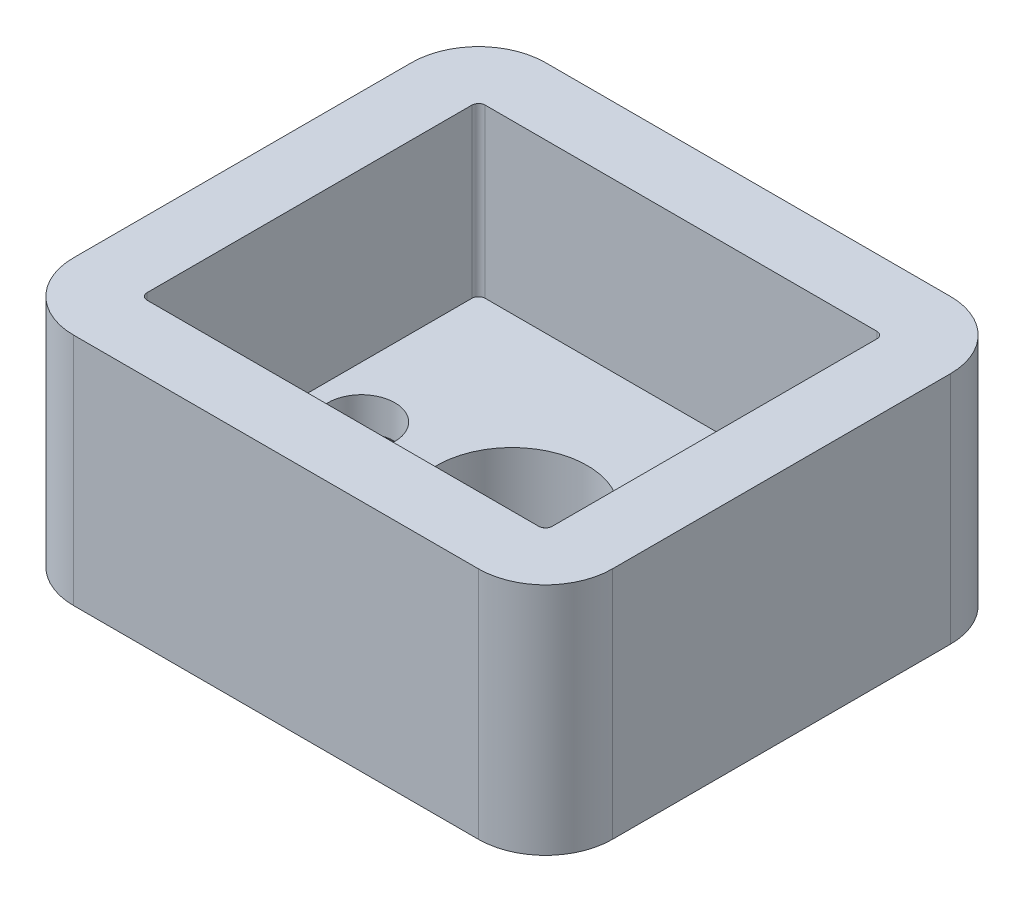
SolidWorks part; units mm, degrees
ref_plane "Front Plane" through (0, 0, 0) normal (0, 0, 1) x (1, 0, 0)
ref_plane "Top Plane" through (0, 0, 0) normal (0, 1, 0) x (1, 0, 0)
ref_plane "Right Plane" through (0, 0, 0) normal (1, 0, 0) x (0, 0, -1)
sketch "Sketch1" plane through (0, 0, 0) normal (0, 1, 0) x (1, 0, 0)
  line L0 (0, 5.05) -> (0, 7.05) construction
  line L1 (-8.05, 7.05) -> (8.05, 7.05)
  line L2 (-8.05, 7.05) -> (-8.05, -7.05)
  line L3 (-8.05, -7.05) -> (8.05, -7.05)
  line L4 (8.05, 7.05) -> (8.05, -7.05)
  line L5 (0, -5.05) -> (0, 0) construction
  line L6 (-8.05, 0) -> (-6.05, 0) construction
  line L11 (0, -5.05) -> (0, 0) construction
  line L12 (0, 0) -> (6.05, 0) construction
  line L13 (0, 0) -> (6.05, 0) construction
  point P4 (0, 0)
  point P233 (0, 0)
  point P296 (0, 0)
  dimension "D1" = 16.1
  dimension "D2" = 14.1
extrude "Boss-Extrude1" add sketch "Sketch1" along normal blind 7
sketch "Sketch3" plane through (0, 7, 0) normal (0, 1, 0) x (1, 0, 0)
  line L0 (-3.85, 0) -> (3.85, 0) construction
  line L1 (-6.05, 5.05) -> (6.05, 5.05)
  line L2 (-6.05, 5.05) -> (-6.05, -5.05)
  line L3 (-6.05, -5.05) -> (6.05, -5.05)
  line L4 (6.05, 5.05) -> (6.05, -5.05)
  line L5 (0, -5.05) -> (0, 5.05) construction
  line L6 (-6.05, 0) -> (6.05, 0) construction
  line L7 (0, -3.85) -> (0, 3.85) construction
  point P4 (0, 0)
  point P316 (0, 0)
  dimension "D1" = 10.1
  dimension "D2" = 12.1
extrude "Cut-Extrude1" cut sketch "Sketch3" against normal offset from surface (5 mm away) 2 up to plane "Top Plane"
hole_wizard "CSK for M1.6 Countersunk Flat Head Screw1" positions "Sketch6" profile "Sketch7" countersink size "M1.6" standard "ISO" end condition up to next
sketch "Sketch6" plane through (0, 0, 0) normal (0, -1, 0) x (-1, 0, 0)
  line L0 (-3.85, 0) -> (3.85, 0) construction
  line L1 (0, 3.85) -> (0, -3.85) construction
  point P0 (4.5, 0)
  point P3 (0, 0)
  point P8 (0, 0)
  point P9 (-4.5, 0)
  dimension "D1" = 4.5
sketch "Sketch7" plane through (-4.5, 0, 0) normal (1, 0, 0) x (0, 0, -1)
  line L0 (0, 0) -> (0, 2)
  line L1 (0, 2) -> (1, 2)
  line L2 (1, 2) -> (1, 1)
  line L3 (1, 1) -> (2, 0)
  line L5 (2, 0) -> (0, 0)
  line L6 (-1, 1) -> (-2, 0) construction
  line L11 (0, -6.35) -> (0, 107.95) construction
  dimension "Thru Hole Dia." = 2
  dimension "Thru Hole Depth" = 2
  dimension "Near C'Sink Dia." = 4
  dimension "Near C'Sink Angle" = 90
sketch "Sketch8" plane through (0, 2, 0) normal (0, 1, 0) x (1, 0, 0)
  circle A0 centre (0, 0) radius 2.25
  dimension "D1" = 4.5
extrude "Cut-Extrude2" cut sketch "Sketch8" against normal through all
fillet "Fillet1" radius 2 4 edges at (-8.05, 3.5, -7.05) (8.05, 3.5, 7.05) (-8.05, 3.5, 7.05) (8.05, 3.5, -7.05)
fillet "Fillet2" radius 0.2 4 edges at (-6.05, 4.5, -5.05) (6.05, 4.5, -5.05) (-6.05, 4.5, 5.05) (6.05, 4.5, 5.05)
